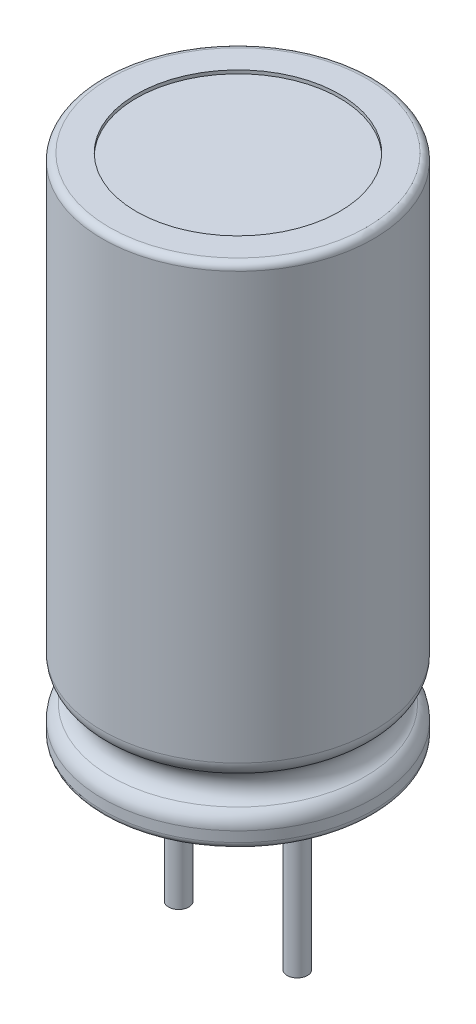
SolidWorks part; units mm, degrees
ref_plane "Front Plane" through (0, 0, 0) normal (0, 0, 1) x (1, 0, 0)
ref_plane "Top Plane" through (0, 0, 0) normal (0, 1, 0) x (1, 0, 0)
ref_plane "Right Plane" through (0, 0, 0) normal (1, 0, 0) x (0, 0, -1)
sketch "Sketch1" plane through (0, 0, 0) normal (0, 0, 1) x (1, 0, 0)
  line L0 (0, 0) -> (0, 15)
  line L1 (0, 15) -> (-4, 15)
  line L2 (-4, 15) -> (-4, 2.2321)
  line L7 (-4, 0) -> (0, 0)
  line L8 (-4, 0.5) -> (-4, 0)
  arc A0 (-4, 2.2321) -> (-3.75, 1.799) centre (-3.5, 2.2321) ccw
  arc A1 (-3.75, 1.799) -> (-3.75, 0.933) centre (-4, 1.366) cw
  arc A2 (-3.75, 0.933) -> (-4, 0.5) centre (-3.5, 0.5) ccw
  point P12 (-4.9013, 1.9492)
  point P13 (0, 0)
  point P14 (-4.4929, 1.3257)
  point P15 (-5, 1.3787)
  point P16 (-4.8001, 1.4056)
  point P17 (-5, 1.3684)
  dimension "D3" = 0.5
  dimension "D4" = 0.5
  dimension "D1" = 4
  dimension "D2" = 15
  dimension "D5" = 0.5
revolve "Revolve1" add sketch "Sketch1" angle 360 about L0
fillet "Fillet2" radius 0.2 2 edges at (0, 0, -4) (0, 15, -4)
sketch "Sketch3" plane through (0, 15, 0) normal (0, 1, 0) x (1, 0, 0)
  line L0 (-3, 0) -> (-4, 0) construction
  circle A2 centre (0, 0) radius 3
  point P3 (-5, 0)
  dimension "D1" = 1
extrude "Cut-Extrude1" cut sketch "Sketch3" against normal blind 0.1
sketch "Sketch4" plane through (0, 0, 0) normal (0, -1, 0) x (1, 0, 0)
  circle A0 centre (0, 0) radius 3
extrude "Cut-Extrude2" cut sketch "Sketch4" against normal blind 0.1
sketch "Sketch2" plane through (0, 0, 0) normal (0, -1, 0) x (1, 0, 0)
  line L0 (1.75, 0) -> (-1.75, 0) construction
  circle A0 centre (-1.75, 0) radius 0.3
  circle A1 centre (1.75, 0) radius 0.3
  point P4 (0, 0)
  dimension "D2" = 0.6
  dimension "D1" = 3.5
extrude "Boss-Extrude1" add sketch "Sketch2" along normal mid plane 10 separate body
